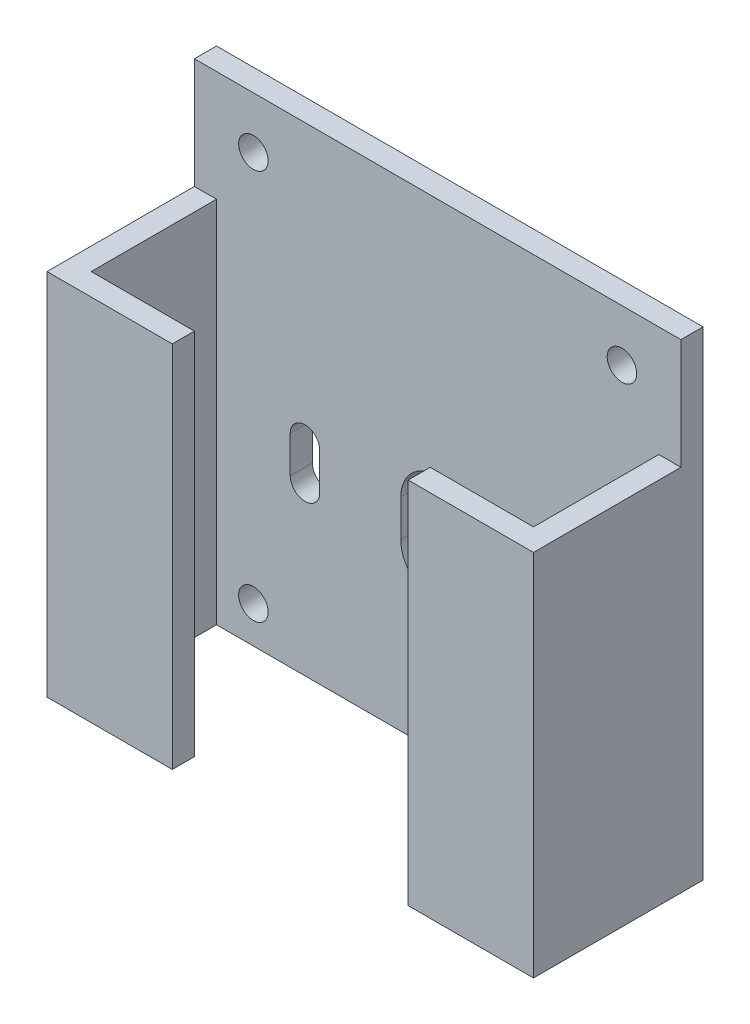
SolidWorks part; units mm, degrees
ref_plane "Front Plane" through (0, 0, 0) normal (0, 0, 1) x (1, 0, 0)
ref_plane "Top Plane" through (0, 0, 0) normal (0, 1, 0) x (1, 0, 0)
ref_plane "Right Plane" through (0, 0, 0) normal (1, 0, 0) x (0, 0, -1)
sketch "Sketch1" plane through (0, 0, 0) normal (1, 0, 0) x (0, 0, -1)
  line L0 (0, 0) -> (0, -65)
  line L1 (0, -65) -> (-23, -65)
  line L2 (-23, -65) -> (-23, 0)
  line L3 (-23, 0) -> (0, 0)
  dimension "D1" = 65
  dimension "D2" = 23
extrude "Boss-Extrude1" add sketch "Sketch1" against normal blind 66
sketch "Sketch2" plane through (0, 0, 0) normal (0, 1, 0) x (1, 0, 0)
  line L0 (-33, 0) -> (-33, -23) construction
  line L1 (-66, 0) -> (0, 0) construction
  line L2 (-66, -23) -> (0, -23) construction
  line L3 (-66, -11.5) -> (0, -11.5) construction
  line L4 (-66, 0) -> (-66, -23) construction
  line L5 (0, 0) -> (0, -23) construction
  line L7 (-63, -20) -> (-3, -20)
  line L8 (-63, -20) -> (-63, -3)
  line L9 (-63, -3) -> (-3, -3)
  line L10 (-3, -20) -> (-3, -3)
  line L11 (-63, -20) -> (-3, -3) construction
  line L12 (-63, -3) -> (-3, -20) construction
  point P12 (-33, -11.5)
  point P17 (-3, -11.5)
  point P18 (-63, -11.5)
  dimension "D1" = 3
  dimension "D2" = 3
  dimension "D3" = 3
  dimension "D4" = 3
extrude "Cut-Extrude1" cut sketch "Sketch2" against normal through all
sketch "Sketch3" plane through (0, 0, 23) normal (0, 0, 1) x (1, 0, 0)
  line L0 (-66, 0) -> (0, 0) construction
  line L1 (-49, 0) -> (-17, 0)
  line L2 (-49, 0) -> (-49, -65)
  line L3 (-49, -65) -> (-17, -65)
  line L4 (-17, 0) -> (-17, -65)
  line L5 (-66, 0) -> (-66, -65) construction
  line L6 (0, 0) -> (0, -65) construction
  dimension "D1" = 17
  dimension "D2" = 17
  dimension "D3" = 32
  dimension "D4" = 65
extrude "Cut-Extrude2" cut sketch "Sketch3" against normal up to next
sketch "Sketch5" plane through (0, 0, 0) normal (0, 0, -1) x (-1, 0, 0)
  line L0 (33, -65) -> (33, 0) construction
  line L1 (66, -65) -> (0, -65) construction
  line L2 (66, 0) -> (0, 0) construction
  line L3 (0, -32.5) -> (66, -32.5) construction
  line L4 (0, -65) -> (0, 0) construction
  line L5 (66, -65) -> (66, 0) construction
  line L6 (66, -37.5) -> (0, -37.5) construction
  line L7 (33, -37.5) -> (33, -42.5) construction
  line L8 (38, -37.5) -> (38, -42.5)
  line L9 (28, -37.5) -> (28, -42.5)
  line L10 (15, -37.5) -> (15, -42.5) construction
  line L11 (17, -37.5) -> (17, -42.5)
  line L12 (13, -37.5) -> (13, -42.5)
  line L13 (51, -37.5) -> (51, -42.5) construction
  line L14 (53, -37.5) -> (53, -42.5)
  line L15 (49, -37.5) -> (49, -42.5)
  circle A1 centre (8, -7) radius 2
  circle A2 centre (58, -7) radius 2
  arc A5 (38, -37.5) -> (28, -37.5) centre (33, -37.5) ccw
  arc A6 (28, -42.5) -> (38, -42.5) centre (33, -42.5) ccw
  arc A7 (17, -37.5) -> (13, -37.5) centre (15, -37.5) ccw
  arc A8 (13, -42.5) -> (17, -42.5) centre (15, -42.5) ccw
  arc A9 (53, -37.5) -> (49, -37.5) centre (51, -37.5) ccw
  arc A10 (49, -42.5) -> (53, -42.5) centre (51, -42.5) ccw
  circle A11 centre (8, -60) radius 2
  circle A12 centre (58, -60) radius 2
  point P22 (15, -40)
  point P24 (33, -40)
  point P34 (51, -40)
  dimension "D2" = 5
  dimension "D7" = 5
  dimension "D8" = 18
  dimension "D12" = 4
  dimension "D13" = 4
  dimension "D18" = 4
  dimension "D19" = 4
  dimension "D20" = 2
  dimension "D21" = 2
  dimension "D22" = 2
  dimension "D23" = 2
  dimension "D24" = 5
  dimension "D1" = 10
  dimension "D3" = 8
  dimension "D4" = 8
  dimension "D5" = 7
  dimension "D6" = 7
  dimension "D9" = 5
  dimension "D10" = 18
  dimension "D11" = 5
  dimension "D14" = 5
  dimension "D15" = 5
  dimension "D16" = 8
  dimension "D17" = 8
extrude "Cut-Extrude3" cut sketch "Sketch5" against normal up to next
sketch "Sketch6" plane through (0, 0, 23) normal (0, 0, 1) x (1, 0, 0)
  line L0 (-49, 0) -> (-49, -65) construction
  line L1 (-66, 0) -> (-49, 0)
  line L2 (-66, 0) -> (-66, -15)
  line L3 (-66, -15) -> (-49, -15)
  line L4 (-49, 0) -> (-49, -15)
  line L5 (0, 0) -> (0, -65) construction
  line L6 (-17, 0) -> (0, 0)
  line L7 (-17, 0) -> (-17, -15)
  line L8 (-17, -15) -> (0, -15)
  line L9 (0, 0) -> (0, -15)
  dimension "D1" = 15
  dimension "D2" = 15
  dimension "D3" = 17
  dimension "D4" = 17
extrude "Cut-Extrude4" cut sketch "Sketch6" against normal up to surface (20 mm away) up to face at (-60, -60, 3)
